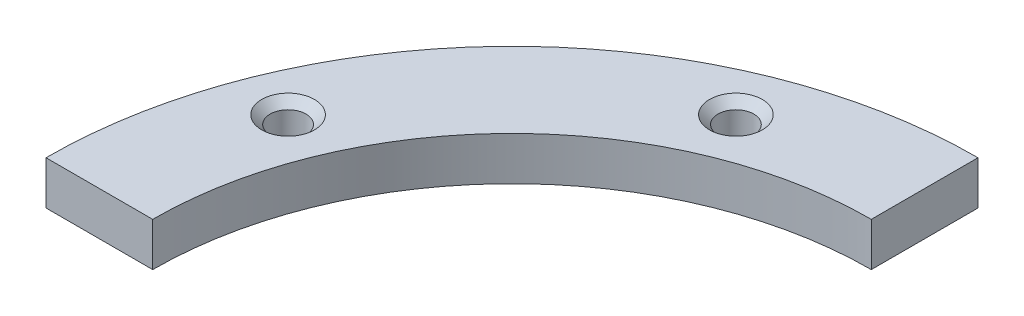
SolidWorks part; units mm, degrees
material "6061-T6 (SS)"
ref_plane "Ebene vorne" through (0, 0, 0) normal (0, 0, 1) x (1, 0, 0)
ref_plane "Ebene oben" through (0, 0, 0) normal (0, 1, 0) x (1, 0, 0)
ref_plane "Ebene rechts" through (0, 0, 0) normal (1, 0, 0) x (0, 0, -1)
sketch "Sketch1" plane through (0, 0, 0) normal (0, 1, 0) x (1, 0, 0)
  line L0 (-33, 0) -> (0, 0) construction
  line L1 (0, 0) -> (0, 33) construction
  line L2 (0, 33) -> (0, 42.8)
  line L3 (-33, 0) -> (-42.8, 0)
  arc A0 (-33, 0) -> (0, 33) centre (0, 0) cw
  arc A1 (-42.8, 0) -> (0, 42.8) centre (0, 0) cw
  dimension "D1" = 90
  dimension "D2" = 42.8
  dimension "D3" = 33
extrude "Boss-Extrude1" add sketch "Sketch1" along normal blind 4
hole_wizard "M4 Tapped Hole1" positions "Sketch2" profile "Sketch3" tap size "M4" standard "DIN" end condition through all
sketch "Sketch2" plane through (0, 4, 0) normal (0, 1, 0) x (1, 0, 0)
  line L0 (-35.1074, 14.542) -> (0, 0) construction
  line L2 (0, 0) -> (-18.3072, 0) construction
  point P0 (-35.1074, 14.542)
  dimension "D1" = 38
  dimension "D2" = 22.5
cosmetic thread "Hole Thread1" parameters "D2"=4
sketch "Sketch3" plane through (-35.1074, 4, -14.542) normal (1, 0, 0) x (0, 0, 1)
  line L0 (0, 0) -> (0, 4)
  line L1 (0, 4) -> (1.65, 4)
  line L2 (1.65, 4) -> (1.65, 0.775)
  line L3 (1.65, 0.775) -> (2.425, 0)
  line L5 (2.425, 0) -> (0, 0)
  line L6 (-1.65, 0.775) -> (-2.425, 0) construction
  line L11 (0, -6.35) -> (0, 107.95) construction
  dimension "Thru Tap Drill Dia." = 3.3
  dimension "Thru Tap Drill Depth" = 4
  dimension "Near C'Sink Dia." = 4.85
  dimension "Near C'Sink Angle" = 90
pattern_circular "CirPattern1" count 8 over 360 about axis through (0, 4, 0) along (0, -1, 0) skipping 1, 2, 3, 4, 5, 6 of "M4 Tapped Hole1"
cosmetic thread "Hole Thread2" parameters "D2"=4
